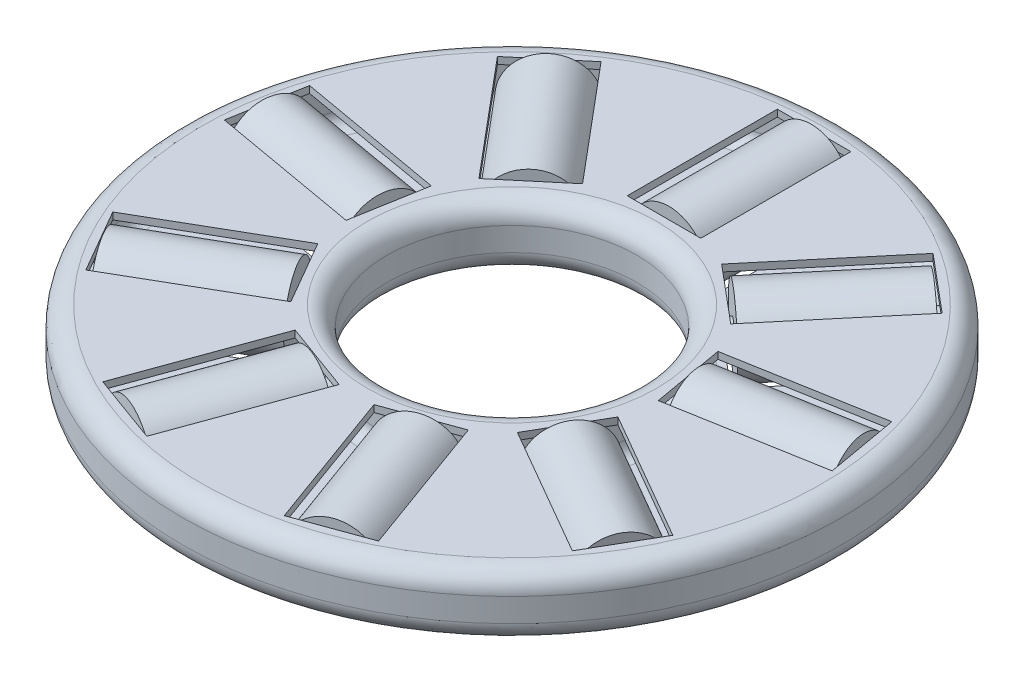
SolidWorks part; units mm, degrees
ref_plane "Front" through (0, 0, 0) normal (0, 0, 1) x (1, 0, 0)
ref_plane "Top" through (0, 0, 0) normal (0, 1, 0) x (1, 0, 0)
ref_plane "Right" through (0, 0, 0) normal (1, 0, 0) x (0, 0, -1)
sketch "Sketch3" plane through (0, 0, 0) normal (0, 0, 1) x (1, 0, 0)
  line L0 (3.2385, 0) -> (8.5344, 0)
  line L1 (3.2385, 0) -> (3.2385, 0.3048)
  line L2 (8.0264, 0.8128) -> (3.7465, 0.8128)
  line L3 (8.5344, 0.3048) -> (8.5344, 0)
  line L4 (0, 0) -> (0, 12.0336) construction
  arc A0 (8.5344, 0.3048) -> (8.0264, 0.8128) centre (8.0264, 0.3048) ccw
  arc A1 (3.7465, 0.8128) -> (3.2385, 0.3048) centre (3.7465, 0.3048) ccw
  point P9 (8.5344, 0.8128)
  dimension "D4" = 0.508
  dimension "D1" = 6.477
  dimension "D2" = 17.0688
  dimension "D3" = 0.8128
revolve "Base-Revolve" add sketch "Sketch3" angle 360 about L4
mirror "Mirror3" about plane through (0, 0, 0) normal (0, 1, 0) of "Base-Revolve"
sketch "Sketch4" plane through (0, 0.8128, 0) normal (0, 1, 0) x (-1, 0, 0)
  line L0 (-0.9525, -7.8232) -> (0.9525, -7.8232)
  line L1 (-0.9525, -7.8232) -> (-0.9525, -3.937)
  line L2 (0.9525, -3.937) -> (-0.9525, -3.937)
  line L3 (0.9525, -3.937) -> (0.9525, -7.8232)
  line L4 (0, 0) -> (0, 21.9042) construction
  dimension "D1" = 3.937
  dimension "D2" = 1.905
  dimension "D3" = 7.8232
extrude "Cut-Extrude1" cut sketch "Sketch4" against normal through all
shell "Shell1" thickness 0.1778
pattern_circular "CirPattern3" count 9 every 40 about axis through (0, 0, 0) along (0, 1, 0) of "Cut-Extrude1"
sketch "Sketch5" plane through (0, 0, 0) normal (1, 0, 0) x (0, 0, -1)
  line L0 (3.3782, 0) -> (8.4328, 0)
  line L1 (4.064, -0.254) -> (4.064, -0.9906)
  line L2 (7.747, -0.9906) -> (4.064, -0.9906)
  line L3 (7.747, -0.9906) -> (7.747, -0.254)
  line L4 (0, 0) -> (20.3368, 0) construction
  line L5 (4.064, -0.254) -> (3.3782, -0.254)
  line L6 (3.3782, 0) -> (3.3782, -0.254)
  line L7 (8.4328, -0.254) -> (7.747, -0.254)
  line L8 (8.4328, -0.254) -> (8.4328, 0)
  dimension "D1" = 0.6858
  dimension "D2" = 4.064
  dimension "D3" = 7.747
  dimension "D4" = 0.6858
  dimension "D5" = 0.254
  dimension "D6" = 1.9812
revolve "Boss-Revolve2" add sketch "Sketch5" angle 360 about L4
pattern_circular "CirPattern2" count 9 every 40 about axis through (0, 0, 0) along (0, 1, 0) of "Boss-Revolve2"
